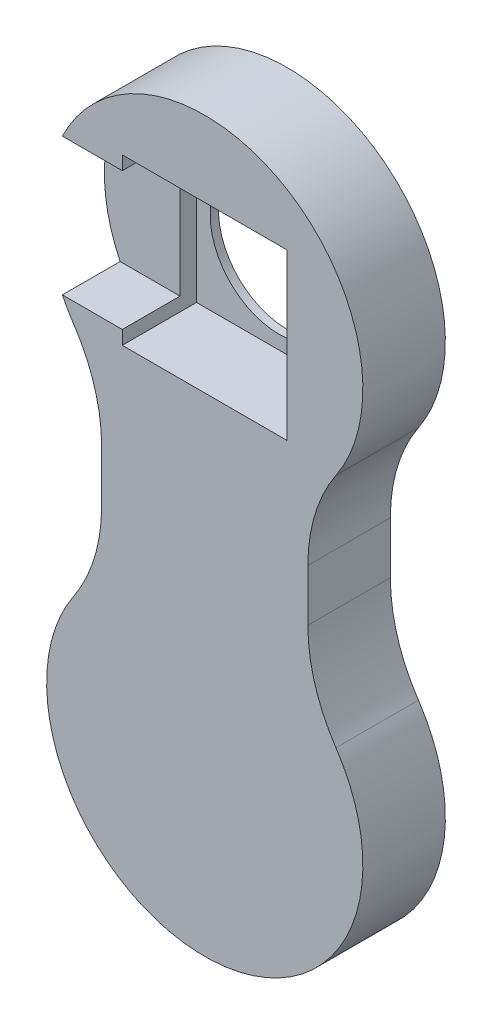
SolidWorks part; units mm, degrees
ref_plane "前基準面" through (0, 0, 0) normal (0, 0, 1) x (1, 0, 0)
ref_plane "上基準面" through (0, 0, 0) normal (0, 1, 0) x (1, 0, 0)
ref_plane "右基準面" through (0, 0, 0) normal (1, 0, 0) x (0, 0, -1)
sketch "Sketch2" plane through (0, 0, 0) normal (0, 0, 1) x (1, 0, 0)
  line L0 (0, 0) -> (0, 150) construction
  line L1 (30, 0) -> (-30, 0) construction
  line L2 (57.5, 0) -> (57.5, 150)
  line L3 (-57.5, 0) -> (-57.5, 150)
  line L4 (-37.5, 43.589) -> (-37.5, 106.411)
  line L5 (37.5, 43.589) -> (37.5, 106.411)
  arc A0 (57.5, 0) -> (-57.5, 0) centre (0, 0) cw
  arc A1 (57.5, 150) -> (-57.5, 150) centre (0, 150) ccw
  circle A2 centre (0, 0) radius 57.5 construction
  circle A3 centre (0, 0) radius 57.5
  circle A4 centre (0, 150) radius 57.5
  dimension "D1" = 150
  dimension "D2" = 20
sketch "Sketch3" plane through (0, 0, 0) normal (0, 0, 1) x (1, 0, 0)
  line L4 (-57.5, 0) -> (-57.5, 150) construction
  line L8 (57.5, 0) -> (57.5, 150) construction
  line L9 (-57.5, 0) -> (-57.5, 150)
  line L10 (57.5, 0) -> (57.5, 150)
  arc A8 (57.5, 150) -> (-57.5, 150) centre (0, 150) ccw construction
  arc A9 (-57.5, 0) -> (57.5, 0) centre (0, 0) ccw construction
  arc A10 (57.5, 150) -> (-57.5, 150) centre (0, 150) ccw
  arc A11 (-57.5, 0) -> (57.5, 0) centre (0, 0) ccw
extrude "Boss-Extrude1" add sketch "Sketch3" along normal blind 30
sketch "Sketch4" plane through (0, 0, 0) normal (0, 0, -1) x (-1, 0, 0)
  line L0 (37.5, 43.589) -> (37.5, 106.411) construction
  line L1 (-37.5, 43.589) -> (-37.5, 106.411) construction
  line L2 (57.5, 0) -> (57.5, 150) construction
  line L3 (-57.5, 0) -> (-57.5, 150) construction
  line L4 (37.5, 43.589) -> (37.5, 106.411)
  line L5 (-37.5, 43.589) -> (-37.5, 106.411)
  line L6 (57.5, 0) -> (57.5, 150)
  line L7 (-57.5, 0) -> (-57.5, 150)
  circle A0 centre (0, 0) radius 57.5 construction
  circle A1 centre (0, 150) radius 57.5 construction
  arc A3 (-57.5, 0) -> (57.5, 0) centre (0, 0) ccw construction
  arc A4 (-37.5, 43.589) -> (-57.5, 0) centre (0, 0) ccw
  arc A5 (-57.5, 150) -> (-37.5, 106.411) centre (0, 150) ccw
  arc A7 (-57.5, 0) -> (57.5, 0) centre (0, 0) ccw
  arc A8 (37.5, 106.411) -> (57.5, 150) centre (0, 150) ccw
  arc A9 (57.5, 0) -> (37.5, 43.589) centre (0, 0) ccw
  line M2 (57.5, 0) -> (57.5, 150)
  line M4 (-57.5, 150) -> (-57.5, 0)
extrude "Cut-Extrude1" cut sketch "Sketch4" against normal blind 35 contours A5 A4 L5 M4 | A9 A8 L4 M2
sketch "Sketch5" plane through (0, 0, 30) normal (0, 0, -1) x (-1, 0, 0)
  line L0 (25, -57.5) -> (-25, -57.5) construction
  line L1 (-30, 120) -> (30, 120)
  line L2 (-30, 120) -> (-30, 180)
  line L3 (-30, 180) -> (30, 180)
  line L4 (30, 120) -> (30, 180)
  line L5 (0, 180) -> (0, 120) construction
  line L6 (-30, 150) -> (30, 150) construction
  line L7 (30, 175) -> (57.5, 175)
  line L8 (30, 175) -> (30, 125)
  line L9 (30, 125) -> (57.5, 125)
  line L10 (57.5, 175) -> (57.5, 125)
  circle A0 centre (0, 150) radius 25
  arc A1 (57.5, 150) -> (-57.5, 150) centre (0, 150) ccw construction
  point P0 (0, 150)
  dimension "D3" = 50
  dimension "D1" = 60
  dimension "D2" = 60
fillet "Fillet1" radius 60 4 edges at (-37.5, 43.589, 15) (-37.5, 106.411, 15) (37.5, 43.589, 15) (37.5, 106.411, 15)
ref_plane "Plane1" through (0, 0, 3) normal (0, 0, -1) x (-1, 0, 0)
sketch "Sketch6" plane through (0, 0, 30) normal (0, 0, 1) x (1, 0, 0)
  circle A0 centre (0, 150) radius 25 construction
  circle A1 centre (0, 150) radius 25
extrude "Cut-Extrude2" cut sketch "Sketch6" against normal through all
sketch "Sketch7" plane through (0, 0, 30) normal (0, 0, 1) x (1, 0, 0)
  line L0 (30, 120) -> (-30, 120) construction
  line L1 (-30, 120) -> (-30, 180) construction
  line L2 (30, 180) -> (-30, 180) construction
  line L3 (30, 120) -> (30, 180) construction
  line L4 (30, 120) -> (-30, 120)
  line L5 (-30, 120) -> (-30, 180)
  line L6 (30, 180) -> (-30, 180)
  line L7 (30, 120) -> (30, 180)
extrude "Cut-Extrude3" cut sketch "Sketch7" against normal up to surface (27 mm away)
sketch "Sketch8" plane through (0, 0, 30) normal (0, 0, 1) x (1, 0, 0)
  line L0 (-30, 125) -> (-57.5, 125) construction
  line L1 (-57.5, 175) -> (-57.5, 125) construction
  line L2 (-30, 175) -> (-57.5, 175) construction
  line L3 (-30, 175) -> (-30, 125) construction
  line L4 (-30, 125) -> (-57.5, 125)
  line L5 (-57.5, 175) -> (-57.5, 125)
  line L6 (-30, 175) -> (-57.5, 175)
  line L7 (-30, 175) -> (-30, 125)
extrude "Cut-Extrude4" cut sketch "Sketch8" against normal offset from surface (21 mm away) 6 up to face at (0, 150, 3)
equation "\"D2@Sketch2\"=\"side thick@零件5-1.Part\""
equation "\"D1@Boss-Extrude1\"=\"thick@零件5-1.Part\""
